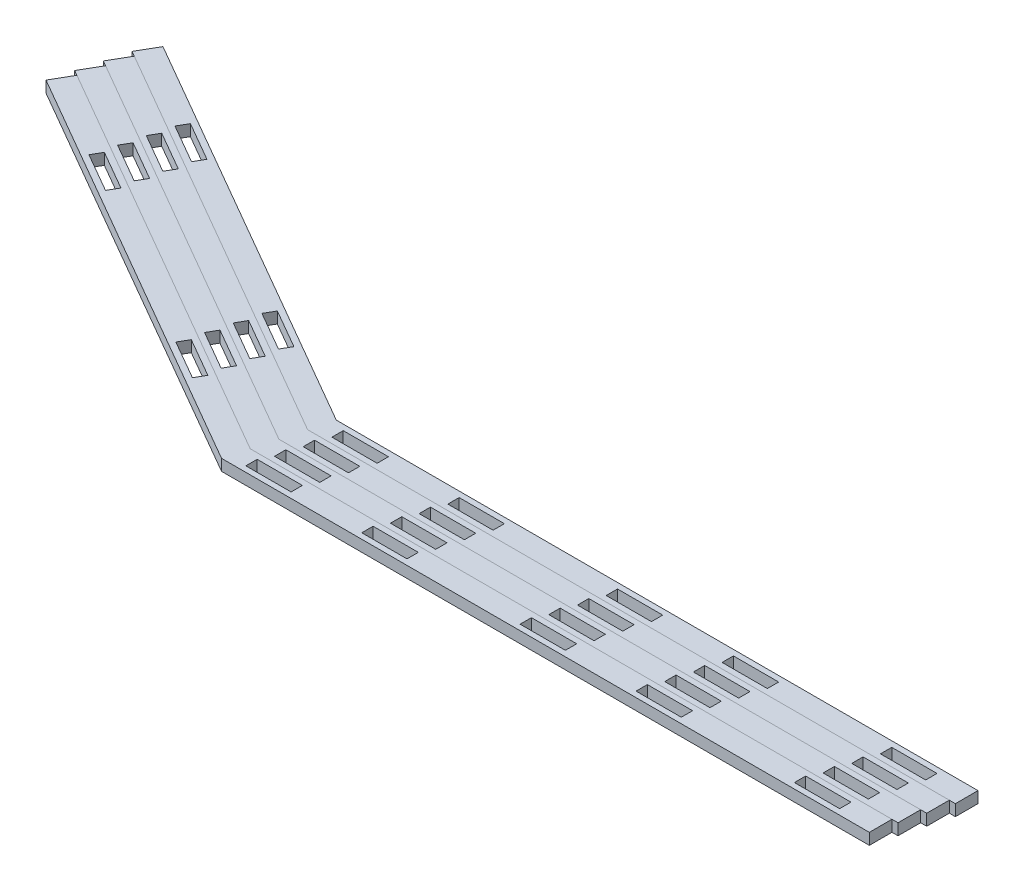
SolidWorks part; units mm, degrees
material "Cedar"
ref_plane "Front Plane" through (0, 0, 0) normal (0, 0, 1) x (1, 0, 0)
ref_plane "Top Plane" through (0, 0, 0) normal (0, 1, 0) x (1, 0, 0)
ref_plane "Right Plane" through (0, 0, 0) normal (1, 0, 0) x (0, 0, -1)
sketch "Sketch4" plane through (0, 0, 0) normal (0, 1, 0) x (1, 0, 0)
  line L0 (-596.8496, 128.2761) -> (-590.4996, 139.2746)
  line L1 (-590.4996, 139.2746) -> (-360.2674, 6.35)
  line L2 (-596.8496, 128.2761) -> (-363.6704, -6.35)
  line L3 (0, -6.35) -> (0, 6.35)
  line L4 (0, 6.35) -> (-360.2674, 6.35)
  line L5 (0, -6.35) -> (-363.6704, -6.35)
  line L6 (-548.5184, 104.0382) -> (-526.5214, 91.3382)
  line L7 (-526.5214, 91.3382) -> (-523.3464, 96.8375)
  line L8 (-523.3464, 96.8375) -> (-545.3434, 109.5375)
  line L9 (-545.3434, 109.5375) -> (-548.5184, 104.0382)
  line L10 (-433.0339, 37.3632) -> (-411.0369, 24.6632)
  line L11 (-411.0369, 24.6632) -> (-407.8619, 30.1625)
  line L12 (-407.8619, 30.1625) -> (-429.8589, 42.8625)
  line L13 (-429.8589, 42.8625) -> (-433.0339, 37.3632)
  line L14 (-353.1983, 3.175) -> (-353.1983, -3.175)
  line L15 (-353.1983, -3.175) -> (-327.7983, -3.175)
  line L16 (-327.7983, -3.175) -> (-327.7983, 3.175)
  line L17 (-327.7983, 3.175) -> (-353.1983, 3.175)
  line L18 (-288.119, 3.175) -> (-288.119, -3.175)
  line L19 (-288.119, -3.175) -> (-262.719, -3.175)
  line L20 (-262.719, -3.175) -> (-262.719, 3.175)
  line L21 (-262.719, 3.175) -> (-288.119, 3.175)
  line L22 (-173.819, -3.175) -> (-173.819, 3.175)
  line L23 (-173.819, 3.175) -> (-199.219, 3.175)
  line L24 (-199.219, 3.175) -> (-199.219, -3.175)
  line L25 (-199.219, -3.175) -> (-173.819, -3.175)
  line L26 (-134.1397, 3.175) -> (-134.1397, -3.175)
  line L27 (-134.1397, -3.175) -> (-108.7397, -3.175)
  line L28 (-108.7397, -3.175) -> (-108.7397, 3.175)
  line L29 (-108.7397, 3.175) -> (-134.1397, 3.175)
  line L30 (-19.8397, -3.175) -> (-19.8397, 3.175)
  line L31 (-19.8397, 3.175) -> (-45.2397, 3.175)
  line L32 (-45.2397, 3.175) -> (-45.2397, -3.175)
  line L33 (-45.2397, -3.175) -> (-19.8397, -3.175)
  point P34 (0, 0)
  dimension "D1" = 12.7
  dimension "D2" = 363.6704
  dimension "D3" = 360.2674
  dimension "D4" = 265.8493
  dimension "D5" = 269.2522
  dimension "D6" = 12.7
  dimension "D7" = 53.975
  dimension "D8" = 6.35
  dimension "D9" = 25.4
  dimension "D10" = 3.175
  dimension "D11" = 25.4
  dimension "D12" = 6.35
  dimension "D13" = 107.95
  dimension "D14" = 25.4
  dimension "D15" = 6.35
  dimension "D16" = 25.4
  dimension "D17" = 6.35
  dimension "D18" = 3.175
  dimension "D19" = 19.8397
  dimension "D20" = 25.4
  dimension "D21" = 6.35
  dimension "D22" = 25.4
  dimension "D23" = 6.35
  dimension "D24" = 3.175
  dimension "D25" = 63.5
  dimension "D26" = 6.35
  dimension "D27" = 25.4
  dimension "D28" = 6.35
  dimension "D29" = 25.4
  dimension "D30" = 3.175
  dimension "D31" = 39.6793
  dimension "D32" = 6.35
  dimension "D33" = 25.4
  dimension "D34" = 6.35
  dimension "D35" = 25.4
  dimension "D36" = 3.175
  dimension "D37" = 63.5
  dimension "D38" = 6.35
  dimension "D39" = 25.4
  dimension "D40" = 6.35
  dimension "D41" = 25.4
  dimension "D42" = 3.175
  dimension "D43" = 39.6793
  dimension "D44" = 6.35
  dimension "D45" = 25.4
  dimension "D46" = 6.35
  dimension "D47" = 25.4
  dimension "D48" = 3.175
extrude "Boss-Extrude2" add sketch "Sketch4" along normal blind 6.35
sketch "Sketch5" plane through (0, 6.35, 0) normal (0, 1, 0) x (1, 0, 0)
  line L0 (-363.6704, -6.35) -> (-360.2674, 6.35) construction
pattern_linear "LPattern1" count 4 spacing 13.148 along (0.2588, 0, -0.9659) of bodies 102
